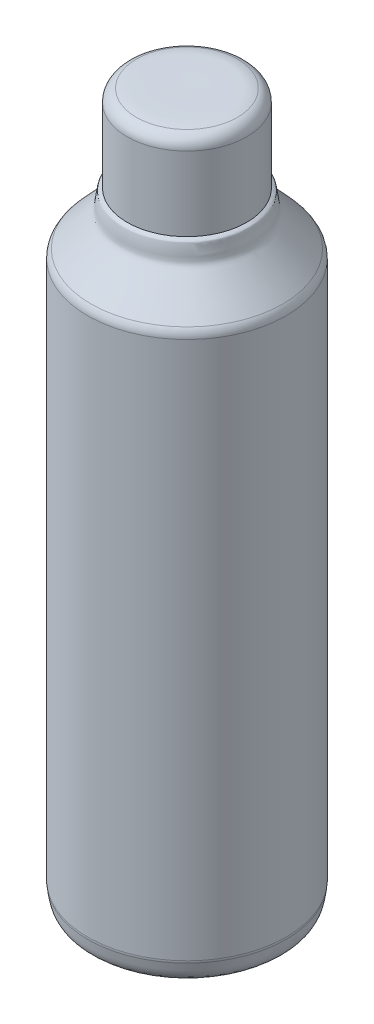
SolidWorks part; units mm, degrees
ref_plane "Front Plane" through (0, 0, 0) normal (0, 0, 1) x (1, 0, 0)
ref_plane "Top Plane" through (0, 0, 0) normal (0, 1, 0) x (1, 0, 0)
ref_plane "Right Plane" through (0, 0, 0) normal (1, 0, 0) x (0, 0, -1)
sketch "Sketch1" plane through (0, 0, 0) normal (0, 0, 1) x (1, 0, 0)
  line L0 (100, 300) -> (500, 300) construction
  line L1 (299.8698, 19.97) -> (299.8698, 581.9306)
  line L2 (222, 42.919) -> (222, 465.0415)
  line L3 (253, 513) -> (253, 571.1365)
  line L4 (222, 351.5689) -> (299.8698, 351.5689) construction
  line L6 (299.8698, 637.8529) -> (299.8698, -18.7553) construction
  arc A0 (222.1477, 41.2064) -> (222, 42.919) centre (232, 42.919) cw
  arc A1 (222, 465.0415) -> (224.6044, 471.7724) centre (232, 465.0415) cw
  arc A2 (253, 571.1365) -> (260.2437, 580.7491) centre (263, 571.1365) cw
  spline S0 degree 3 poles (260.2437, 580.7491) (263.083, 581.5632) (266.0594, 581.9728) (269, 582.0091) (279.2894, 582.1361) (289.5799, 582.0845) (299.8698, 581.9306) knots 1.21089 1.21089 1.21089 1.21089 2 2 2 2.440962 2.440962 2.440962 2.440962
  spline S2 degree 3 poles (224.6044, 471.7724) (231.3644, 479.2) (238.4049, 486.4628) (245, 494) (246.0975, 495.2543) (247.381, 496.4525) (248, 498) (248.753, 499.8826) (248.5752, 502.0174) (249, 504) (250.8319, 512.5486) (248.6361, 510.818) (253, 513) knots 1.073552 1.073552 1.073552 1.073552 2 2 2 3 3 3 4 4 4 5 5 5 5
  spline S3 degree 2 poles (299.8698, 19.97) (245.2692, 19.9064) (227.7082, 27.1927) knots 0 0 0 0.45569 0.45569 0.45569
  spline S5 degree 3 poles (227.7082, 27.1927) (223.0015, 30.4172) (223.0126, 36.2314) (222.1477, 41.2064) knots 8.018855 8.018855 8.018855 8.018855 8.950003 8.950003 8.950003 8.950003
  point P16 (0, 0)
  dimension "D1" = 10
  dimension "D2" = 10
  dimension "D3" = 10
revolve "Revolve1" add sketch "Sketch1" angle 360 about L1
